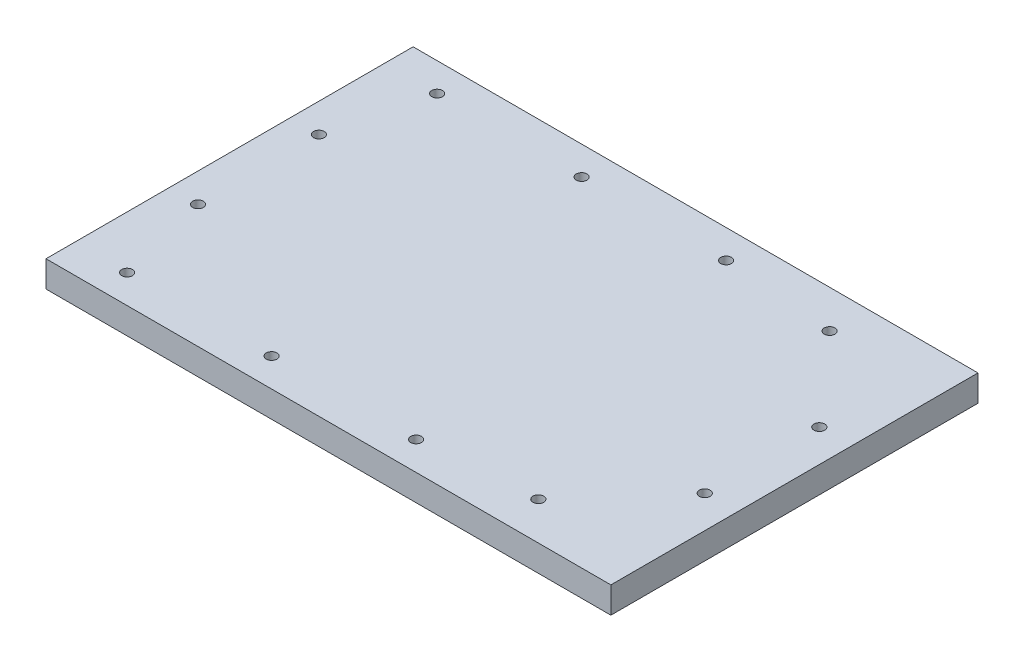
SolidWorks part; units mm, degrees
ref_plane "Front Plane" through (0, 0, 0) normal (0, 0, 1) x (1, 0, 0)
ref_plane "Top Plane" through (0, 0, 0) normal (0, 1, 0) x (1, 0, 0)
ref_plane "Right Plane" through (0, 0, 0) normal (1, 0, 0) x (0, 0, -1)
sketch "Sketch2" plane through (0, 0, 0) normal (0, 1, 0) x (1, 0, 0)
  line L1 (215, -0.1336) -> (0, -0.1336)
  line L2 (215, -0.1336) -> (215, -139.8664)
  line L3 (0, -0.1336) -> (0, -139.8664)
  line L4 (215, -139.8664) -> (0, -139.8664)
  line L5 (215, -0.1336) -> (0, -139.8664) construction
  line L6 (0, -0.1336) -> (215, -139.8664) construction
  point P4 (107.5, -70)
extrude "Boss-Extrude1" add sketch "Sketch2" along normal blind 10
sketch "Sketch3" plane through (0, 0, 0) normal (0, 1, 0) x (1, 0, 0)
  circle A0 centre (20, -129) radius 2.05
  circle A1 centre (75, -129) radius 2.05
  circle A2 centre (130, -129) radius 2.05
  circle A3 centre (172.961, -125.4328) radius 2.05
  circle A4 centre (202.6611, -91.813) radius 2.05
  circle A5 centre (202.6611, -48.187) radius 2.05
  circle A6 centre (172.961, -14.5672) radius 2.05
  circle A7 centre (130, -11) radius 2.05
  circle A8 centre (75, -11) radius 2.05
  circle A9 centre (20, -11) radius 2.05
  circle A10 centre (11, -47) radius 2.05
  circle A11 centre (11, -93) radius 2.05
extrude "Cut-Extrude2" cut sketch "Sketch3" against normal through all and the other way through all
